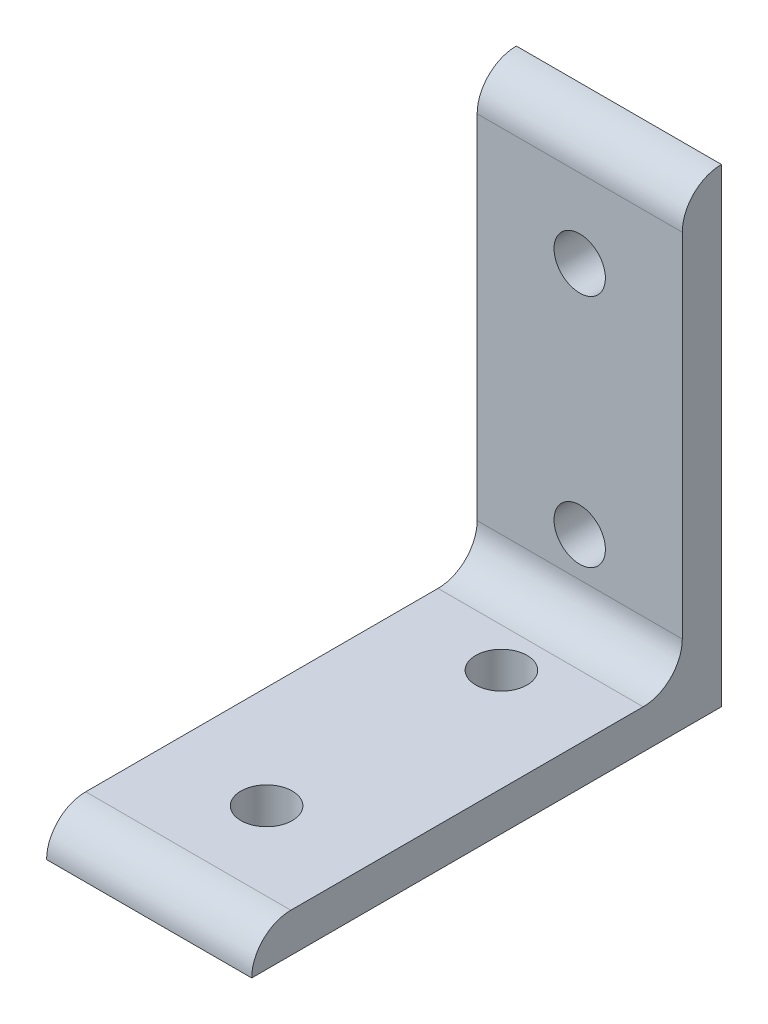
SolidWorks part; units mm, degrees
ref_plane "Front"
ref_plane "Top" through (0, 0, 0) normal (0, 1, 0) x (1, 0, 0)
ref_plane "Right" through (0, 0, 0) normal (1, 0, 0) x (0, 0, -1)
sketch "Sketch1" plane through (0, 0, 0) normal (1, 0, 0) x (0, 0, -1)
  line L0 (-6.35, 12.7) -> (-6.35, 69.85)
  line L1 (-69.85, 6.35) -> (-12.7, 6.35)
  line L6 (0, 0) -> (0, 76.2)
  line L7 (-76.2, 0) -> (0, 0)
  arc A0 (-12.7, 6.35) -> (-6.35, 12.7) centre (-12.7, 12.7) ccw
  arc A1 (0, 76.2) -> (-6.35, 69.85) centre (0, 69.85) ccw
  arc A2 (-69.85, 6.35) -> (-76.2, 0) centre (-69.85, 0) ccw
  dimension "InnerRadius" = 6.35
  dimension "LengthZ" = 76.2
  dimension "HeightY" = 76.2
  dimension "Thick" = 6.35
extrude "Base Extrude" add sketch "Sketch1" against normal mid plane 33.274
sketch "Sketch2" plane through (0, 0, 0) normal (0, -1, 0) x (1, 0, 0)
  line L0 (-16.637, 0) -> (16.637, 0) construction
  line L1 (-16.637, 76.2) -> (-16.637, 0) construction
  circle A1 centre (0, 19.05) radius 4.1656
  dimension "Hole1Diam" = 8.3312
  dimension "Hole1Z" = 19.05
  dimension "Hole1X" = 16.637
extrude "Hole1" cut sketch "Sketch2" against normal through all
pattern_linear "Hole1 Pattern" count 2 spacing 38.1 along (0, 0, 1) of "Hole1"
sketch "Sketch3" plane through (0, 0, 0) normal (0, 0, -1) x (-1, 0, 0)
  line L0 (16.637, 0) -> (-16.637, 0) construction
  line L1 (16.637, 0) -> (16.637, 76.2) construction
  circle A0 centre (0, 19.05) radius 4.1656
  dimension "Hole2Diam" = 8.3312
  dimension "Hole2Y" = 19.05
  dimension "Hole2X" = 16.637
extrude "Hole2" cut sketch "Sketch3" against normal through all
pattern_linear "Hole2 Pattern" count 2 spacing 38.1 along (0, 1, 0) of "Hole2"
sketch "Sketch4" plane through (0, 0, 0) normal (0, 0, -1) x (-1, 0, 0)
  line L0 (16.637, 76.2) -> (-2.413, 76.2)
  line L1 (16.637, 76.2) -> (-16.637, 76.2) construction
  line L2 (-2.413, 76.2) -> (16.637, 12.7)
  line L3 (16.637, 0) -> (16.637, 76.2) construction
  line L4 (16.637, 12.7) -> (16.637, 76.2)
  dimension "Corner1X" = 19.05
  dimension "D2" = 63.5
extrude "Corner Cut 1" [suppressed] cut sketch "Sketch4" against normal through all
sketch "Sketch5" plane through (0, 0, 0) normal (0, 0, -1) x (-1, 0, 0)
  line L0 (2.413, 76.2) -> (-16.637, 76.2)
  line L1 (16.637, 76.2) -> (-16.637, 76.2) construction
  line L2 (-16.637, 76.2) -> (-16.637, 12.7)
  line L3 (-16.637, 0) -> (-16.637, 76.2) construction
  line L4 (-16.637, 12.7) -> (2.413, 76.2)
  dimension "Corner2X" = 19.05
  dimension "D2" = 63.5
extrude "Corner Cut 2" [suppressed] cut sketch "Sketch5" against normal through all
